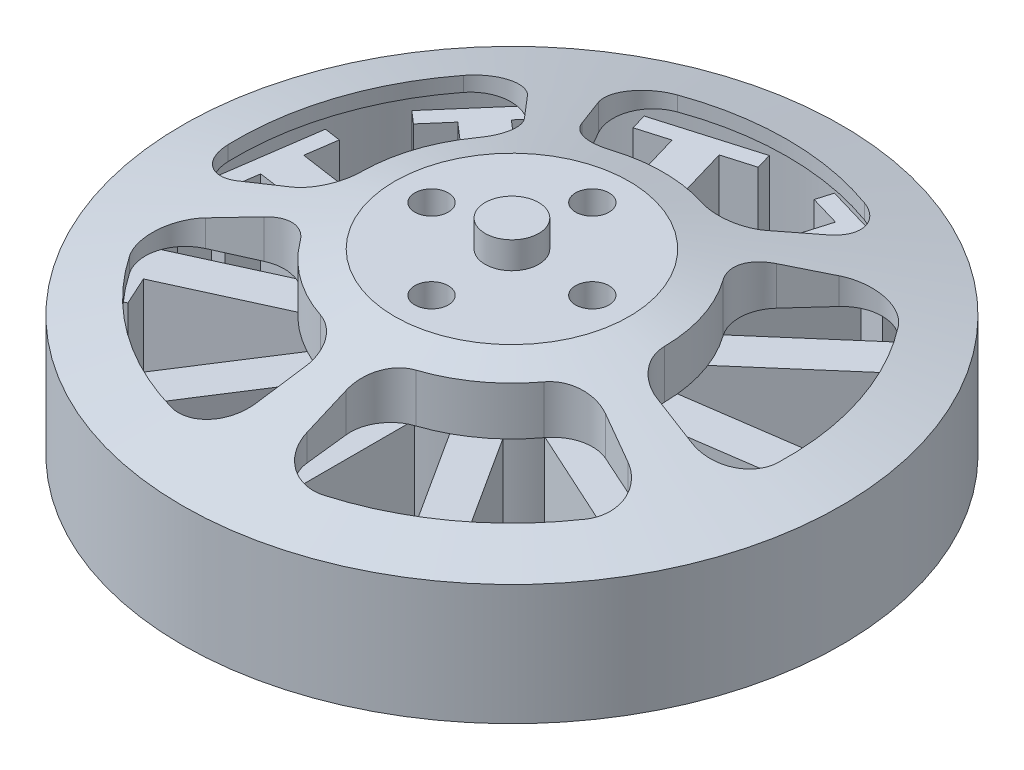
SolidWorks part; units mm, degrees
material "6061-T6 (SS)"
ref_plane "Alzado" through (0, 0, 0) normal (0, 0, 1) x (1, 0, 0)
ref_plane "Planta" through (0, 0, 0) normal (0, 1, 0) x (1, 0, 0)
ref_plane "Vista lateral" through (0, 0, 0) normal (1, 0, 0) x (0, 0, -1)
sketch "Croquis1" plane through (0, 0, 0) normal (0, 1, 0) x (1, 0, 0)
  circle A0 centre (0, 0) radius 24.6
  dimension "D1" = 49.2
extrude "Saliente-Extruir1" add sketch "Croquis1" along normal blind 9
sketch "Croquis2" plane through (0, 0, 0) normal (0, 0, 1) x (1, 0, 0)
  line L0 (-24.6, 9) -> (-8.75, 13.3)
  line L1 (-8.75, 13.3) -> (0, 13.3)
  line L2 (0, 13.3) -> (0, 9)
  line L3 (24.6, 9) -> (-24.6, 9) construction
  line L4 (0, 9) -> (-24.6, 9)
  dimension "D1" = 8.75
  dimension "D2" = 4.3
revolve "Revolución1" add sketch "Croquis2" angle 360 about L2
sketch "Croquis4" plane through (0, 0, 0) normal (0, -1, 0) x (1, 0, 0)
  circle A0 centre (0, 0) radius 22.8389
extrude "Cortar-Extruir1" cut sketch "Croquis4" against normal blind 9
sketch "Croquis5" plane through (0, 13.3, 0) normal (0, 1, 0) x (1, 0, 0)
  line L0 (-8.5704, 15.019) -> (-6.9301, 12.1446)
  line L1 (6.9301, 12.1446) -> (8.5704, 15.019)
  line L2 (0, 0) -> (0, 27.6667) construction
  line L3 (11.6356, 12.7921) -> (9.4086, 10.3438)
  line L4 (13.6917, -2.8381) -> (16.9324, -3.5098)
  line L5 (15.7616, -7.1131) -> (12.745, -5.7517)
  line L6 (1.5318, -13.8986) -> (1.8944, -17.1882)
  line L7 (-1.8944, -17.1882) -> (-1.5318, -13.8986)
  line L8 (-12.745, -5.7517) -> (-15.7616, -7.1131)
  line L9 (-16.9324, -3.5098) -> (-13.6917, -2.8381)
  line L10 (-9.4086, 10.3438) -> (-11.6356, 12.7921)
  arc A0 (3.4173, 10.7719) -> (-3.4173, 10.7719) centre (0, 0) ccw
  arc A1 (6.9844, 19.3273) -> (-6.9844, 19.3273) centre (0, 0) ccw
  arc A2 (6.9301, 12.1446) -> (3.4173, 10.7719) centre (4.3245, 13.6314) cw
  arc A3 (-6.9301, 12.1446) -> (-3.4173, 10.7719) centre (-4.3245, 13.6314) ccw
  arc A4 (8.5704, 15.019) -> (6.9844, 19.3273) centre (5.9648, 16.5059) ccw
  arc A5 (-8.5704, 15.019) -> (-6.9844, 19.3273) centre (-5.9648, 16.5059) cw
  arc A6 (11.3007, 0.0786) -> (9.1887, 6.5788) centre (0, 0) ccw
  arc A7 (20.5397, -0.6701) -> (16.2231, 12.615) centre (0, 0) ccw
  arc A8 (13.6917, -2.8381) -> (11.3007, 0.0786) centre (14.3006, 0.0995) cw
  arc A9 (9.4086, 10.3438) -> (9.1887, 6.5788) centre (11.6279, 8.3252) ccw
  arc A10 (16.9324, -3.5098) -> (20.5397, -0.6701) centre (17.5413, -0.5723) ccw
  arc A11 (11.6356, 12.7921) -> (16.2231, 12.615) centre (13.8548, 10.7735) cw
  arc A12 (3.5669, -10.7233) -> (9.0962, -6.706) centre (0, 0) ccw
  arc A13 (5.7098, -19.7415) -> (17.0108, -11.5308) centre (0, 0) ccw
  arc A14 (1.5318, -13.8986) -> (3.5669, -10.7233) centre (4.5137, -13.57) cw
  arc A15 (12.745, -5.7517) -> (9.0962, -6.706) centre (11.511, -8.4862) ccw
  arc A16 (1.8944, -17.1882) -> (5.7098, -19.7415) centre (4.8763, -16.8596) ccw
  arc A17 (15.7616, -7.1131) -> (17.0108, -11.5308) centre (14.5276, -9.8475) cw
  arc A18 (-9.0962, -6.706) -> (-3.5669, -10.7233) centre (0, 0) ccw
  arc A19 (-17.0108, -11.5308) -> (-5.7098, -19.7415) centre (0, 0) ccw
  arc A20 (-12.745, -5.7517) -> (-9.0962, -6.706) centre (-11.511, -8.4862) cw
  arc A21 (-1.5318, -13.8986) -> (-3.5669, -10.7233) centre (-4.5137, -13.57) ccw
  arc A22 (-15.7616, -7.1131) -> (-17.0108, -11.5308) centre (-14.5276, -9.8475) ccw
  arc A23 (-1.8944, -17.1882) -> (-5.7098, -19.7415) centre (-4.8763, -16.8596) cw
  arc A24 (-9.1887, 6.5788) -> (-11.3007, 0.0786) centre (0, 0) ccw
  arc A25 (-16.2231, 12.615) -> (-20.5397, -0.6701) centre (0, 0) ccw
  arc A26 (-9.4086, 10.3438) -> (-9.1887, 6.5788) centre (-11.6279, 8.3252) cw
  arc A27 (-13.6917, -2.8381) -> (-11.3007, 0.0786) centre (-14.3006, 0.0995) ccw
  arc A28 (-11.6356, 12.7921) -> (-16.2231, 12.615) centre (-13.8548, 10.7735) ccw
  arc A29 (-16.9324, -3.5098) -> (-20.5397, -0.6701) centre (-17.5413, -0.5723) cw
  point P65 (0, 0)
  dimension "D1" = 3
  dimension "D2" = 5
extrude "Cortar-Extruir2" cut sketch "Croquis5" against normal through all
sketch "Croquis3" plane through (0, 13.3, 0) normal (0, 1, 0) x (1, 0, 0)
  circle A0 centre (0, 0) radius 2
  dimension "D1" = 4
extrude "Saliente-Extruir2" add sketch "Croquis3" along normal blind 8 from offset 6 offset against normal yes
sketch "Croquis6" plane through (0, 7.3, 0) normal (0, -1, 0) x (1, 0, 0)
  line L0 (-1.4178, 20.2309) -> (-1.4178, 8.6919)
  line L1 (1.4178, 20.2309) -> (1.4178, 8.6919)
  line L2 (0, 0) -> (0, 19.3794) construction
  line L3 (-1.4178, 20.2309) -> (-3.7639, 20.2309)
  line L4 (-3.7639, 20.2309) -> (-3.7639, 21.4518)
  line L5 (-3.7639, 21.4518) -> (3.7639, 21.4518)
  line L6 (3.7639, 21.4518) -> (3.7639, 20.2309)
  line L7 (3.7639, 20.2309) -> (1.4178, 20.2309)
  line L8 (9.745, 17.7858) -> (3.5065, 8.0786)
  line L9 (12.1304, 16.2528) -> (5.8919, 6.5456)
  line L10 (9.745, 17.7858) -> (7.7713, 19.0542)
  line L11 (7.7713, 19.0542) -> (8.4313, 20.0813)
  line L12 (8.4313, 20.0813) -> (14.7641, 16.0115)
  line L13 (14.7641, 16.0115) -> (14.1041, 14.9844)
  line L14 (14.1041, 14.9844) -> (12.1304, 16.2528)
  line L15 (17.8137, 9.6939) -> (7.3175, 4.9004)
  line L16 (18.9916, 7.1146) -> (8.4954, 2.3211)
  line L17 (17.8137, 9.6939) -> (16.8391, 11.828)
  line L18 (16.8391, 11.828) -> (17.9496, 12.3352)
  line L19 (17.9496, 12.3352) -> (21.0768, 5.4876)
  line L20 (21.0768, 5.4876) -> (19.9663, 4.9805)
  line L21 (19.9663, 4.9805) -> (18.9916, 7.1146)
  line L22 (20.2268, -1.4758) -> (8.8052, 0.1663)
  line L23 (19.8232, -4.2825) -> (8.4017, -2.6403)
  line L24 (20.2268, -1.4758) -> (20.5606, 0.8464)
  line L25 (20.5606, 0.8464) -> (21.7691, 0.6727)
  line L26 (21.7691, 0.6727) -> (20.6978, -6.7785)
  line L27 (20.6978, -6.7785) -> (19.4893, -6.6047)
  line L28 (19.4893, -6.6047) -> (19.8232, -4.2825)
  line L29 (16.2179, -12.177) -> (7.4974, -4.6205)
  line L30 (14.3611, -14.3199) -> (5.6405, -6.7635)
  line L31 (16.2179, -12.177) -> (17.7543, -10.4039)
  line L32 (17.7543, -10.4039) -> (18.677, -11.2034)
  line L33 (18.677, -11.2034) -> (13.7473, -16.8925)
  line L34 (13.7473, -16.8925) -> (12.8247, -16.093)
  line L35 (12.8247, -16.093) -> (14.3611, -14.3199)
  line L36 (7.06, -19.012) -> (3.8091, -7.9404)
  line L37 (4.3394, -19.8108) -> (1.0885, -8.7393)
  line L38 (7.06, -19.012) -> (9.3111, -18.351)
  line L39 (9.3111, -18.351) -> (9.6551, -19.5224)
  line L40 (9.6551, -19.5224) -> (2.4322, -21.6432)
  line L41 (2.4322, -21.6432) -> (2.0883, -20.4718)
  line L42 (2.0883, -20.4718) -> (4.3394, -19.8108)
  line L43 (-4.3394, -19.8108) -> (-1.0885, -8.7393)
  line L44 (-7.06, -19.012) -> (-3.8091, -7.9404)
  line L45 (-4.3394, -19.8108) -> (-2.0883, -20.4718)
  line L46 (-2.0883, -20.4718) -> (-2.4322, -21.6432)
  line L47 (-2.4322, -21.6432) -> (-9.6551, -19.5224)
  line L48 (-9.6551, -19.5224) -> (-9.3111, -18.351)
  line L49 (-9.3111, -18.351) -> (-7.06, -19.012)
  line L50 (-14.3611, -14.3199) -> (-5.6405, -6.7635)
  line L51 (-16.2179, -12.177) -> (-7.4974, -4.6205)
  line L52 (-14.3611, -14.3199) -> (-12.8247, -16.093)
  line L53 (-12.8247, -16.093) -> (-13.7473, -16.8925)
  line L54 (-13.7473, -16.8925) -> (-18.677, -11.2034)
  line L55 (-18.677, -11.2034) -> (-17.7543, -10.4039)
  line L56 (-17.7543, -10.4039) -> (-16.2179, -12.177)
  line L57 (-19.8232, -4.2825) -> (-8.4017, -2.6403)
  line L58 (-20.2268, -1.4758) -> (-8.8052, 0.1663)
  line L59 (-19.8232, -4.2825) -> (-19.4893, -6.6047)
  line L60 (-19.4893, -6.6047) -> (-20.6978, -6.7785)
  line L61 (-20.6978, -6.7785) -> (-21.7691, 0.6727)
  line L62 (-21.7691, 0.6727) -> (-20.5606, 0.8464)
  line L63 (-20.5606, 0.8464) -> (-20.2268, -1.4758)
  line L64 (-18.9916, 7.1146) -> (-8.4954, 2.3211)
  line L65 (-17.8137, 9.6939) -> (-7.3175, 4.9004)
  line L66 (-18.9916, 7.1146) -> (-19.9663, 4.9805)
  line L67 (-19.9663, 4.9805) -> (-21.0768, 5.4876)
  line L68 (-21.0768, 5.4876) -> (-17.9496, 12.3352)
  line L69 (-17.9496, 12.3352) -> (-16.8391, 11.828)
  line L70 (-16.8391, 11.828) -> (-17.8137, 9.6939)
  line L71 (-12.1304, 16.2528) -> (-5.8919, 6.5456)
  line L72 (-9.745, 17.7858) -> (-3.5065, 8.0786)
  line L73 (-12.1304, 16.2528) -> (-14.1041, 14.9844)
  line L74 (-14.1041, 14.9844) -> (-14.7641, 16.0115)
  line L75 (-14.7641, 16.0115) -> (-8.4313, 20.0813)
  line L76 (-8.4313, 20.0813) -> (-7.7713, 19.0542)
  line L77 (-7.7713, 19.0542) -> (-9.745, 17.7858)
  arc A0 (-5.8919, 6.5456) -> (-7.3175, 4.9004) centre (0, 0) ccw
  arc A1 (3.5065, 8.0786) -> (1.4178, 8.6919) centre (0, 0) ccw
  arc A2 (7.3175, 4.9004) -> (5.8919, 6.5456) centre (0, 0) ccw
  arc A3 (8.8052, 0.1663) -> (8.4954, 2.3211) centre (0, 0) ccw
  arc A4 (7.4974, -4.6205) -> (8.4017, -2.6403) centre (0, 0) ccw
  arc A5 (3.8091, -7.9404) -> (5.6405, -6.7635) centre (0, 0) ccw
  arc A6 (-1.0885, -8.7393) -> (1.0885, -8.7393) centre (0, 0) ccw
  arc A7 (-5.6405, -6.7635) -> (-3.8091, -7.9404) centre (0, 0) ccw
  arc A8 (-8.4017, -2.6403) -> (-7.4974, -4.6205) centre (0, 0) ccw
  arc A10 (-8.4954, 2.3211) -> (-8.8052, 0.1663) centre (0, 0) ccw
  arc A11 (-1.4178, 8.6919) -> (-3.5065, 8.0786) centre (0, 0) ccw
  point P93 (0, 0)
  dimension "D1" = 11
extrude "Saliente-Extruir3" add sketch "Croquis6" along normal blind 8
sketch "Croquis7" plane through (0, -0.7, 0) normal (0, -1, 0) x (1, 0, 0)
  circle A0 centre (0, 0) radius 7.5
  dimension "D1" = 15
extrude "Saliente-Extruir4" add sketch "Croquis7" along normal blind 5
sketch "Croquis8" plane through (0, -5.7, 0) normal (0, -1, 0) x (1, 0, 0)
  circle A0 centre (0, 0) radius 12.25
  dimension "D1" = 24.5
extrude "Saliente-Extruir5" add sketch "Croquis8" along normal blind 1.2
sketch "Croquis9" plane through (0, -6.9, 0) normal (0, -1, 0) x (1, 0, 0)
  circle A0 centre (0, 0) radius 2
  dimension "D1" = 4
extrude "Saliente-Extruir6" add sketch "Croquis9" along normal blind 1.8
sketch "Croquis10" plane through (0, -6.9, 0) normal (0, -1, 0) x (1, 0, 0)
  line L0 (-1.85, 4.2703) -> (-1.85, 1.6815)
  line L1 (1.85, 4.2703) -> (1.85, 1.6815)
  line L2 (-1.85, 4.2703) -> (1.85, 4.2703)
  line L3 (0, 0) -> (0, 5.3901) construction
  arc A0 (-1.85, 1.6815) -> (1.85, 1.6815) centre (0, 0) ccw
  point P7 (0, 4.2703)
  dimension "D1" = 3.7
  dimension "D2" = 5
extrude "Saliente-Extruir7" add sketch "Croquis10" along normal blind 0.8
sketch "Croquis11" plane through (0, 13.3, 0) normal (0, 1, 0) x (1, 0, 0)
  circle A0 centre (0, 0) radius 6 construction
  circle A1 centre (0, -6) radius 1.25
  circle A2 centre (6, 0) radius 1.25
  circle A3 centre (0, 6) radius 1.25
  circle A4 centre (-6, 0) radius 1.25
  dimension "D1" = 12
  dimension "D2" = 2.5
extrude "Cortar-Extruir3" cut sketch "Croquis11" against normal blind 3
sketch "Croquis12" plane through (0, -6.9, 0) normal (0, -1, 0) x (1, 0, 0)
  line L0 (0, -8) -> (0, 8) construction
  line L1 (-9.5, 0) -> (9.5, 0) construction
  circle A0 centre (0, 8) radius 1.3484
  circle A1 centre (0, -8) radius 1.3484
  circle A2 centre (-9.5, 0) radius 1.3484
  circle A3 centre (9.5, 0) radius 1.3484
  point P4 (0, 0)
  point P10 (0, 0)
  dimension "D1" = 16
  dimension "D2" = 19
extrude "Cortar-Extruir4" cut sketch "Croquis12" against normal blind 6
sketch "Croquis13" plane through (0, -5.7, 0) normal (0, 1, 0) x (1, 0, 0)
  line L0 (-6.9089, 2.7478) -> (-3.1846, 6.4721)
  line L1 (-3.1846, 6.4721) -> (-16.0348, 19.3223)
  line L2 (-16.0348, 19.3223) -> (-19.7591, 15.598)
  line L3 (-19.7591, 15.598) -> (-6.9089, 2.7478)
extrude "Saliente-Extruir8" add sketch "Croquis13" along normal blind 2 from offset 1
